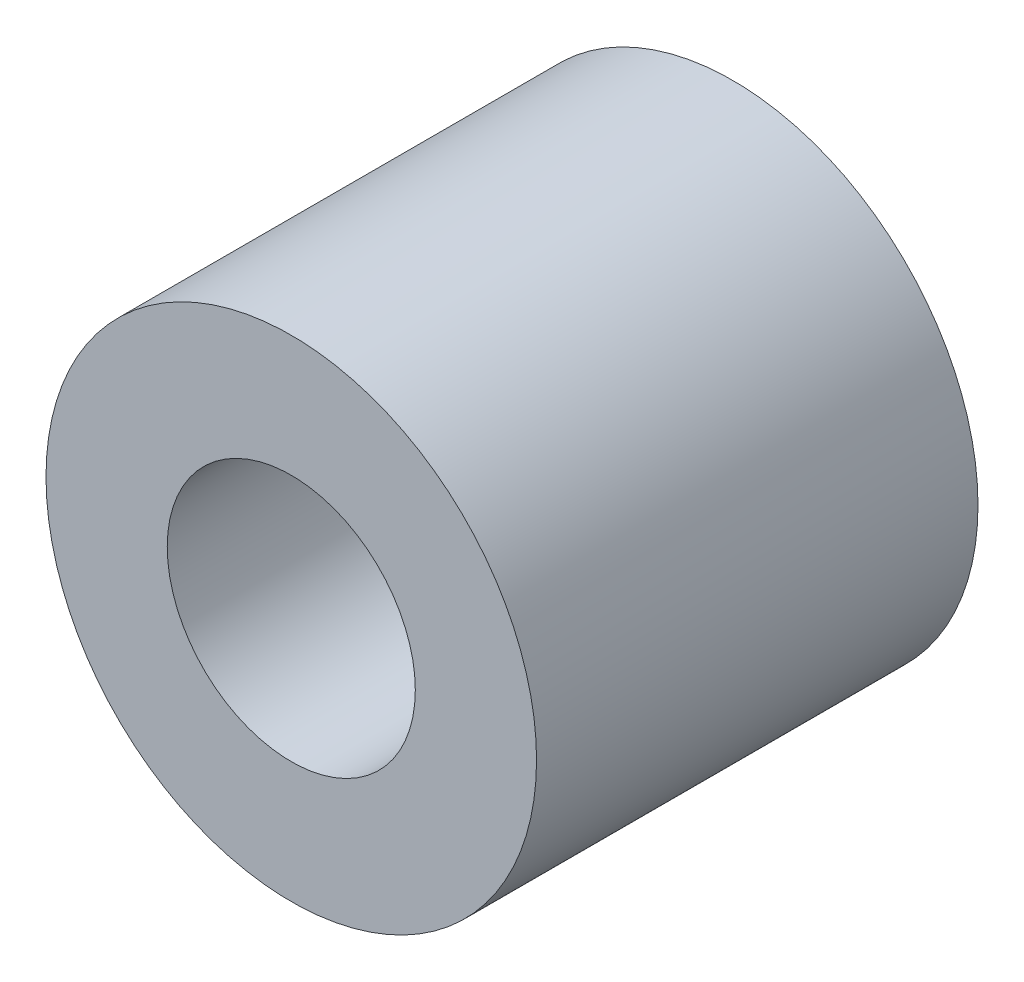
SolidWorks part; units mm, degrees
ref_plane "Front Plane" through (0, 0, 0) normal (0, 0, 1) x (1, 0, 0)
ref_plane "Top Plane" through (0, 0, 0) normal (0, 1, 0) x (1, 0, 0)
ref_plane "Right Plane" through (0, 0, 0) normal (1, 0, 0) x (0, 0, -1)
sketch "Sketch1" plane through (0, 0, 0) normal (0, 0, 1) x (1, 0, 0)
  circle A0 centre (0, 0) radius 4.445
  dimension "D1" = 8.89
extrude "Boss-Extrude1" add sketch "Sketch1" along normal mid plane 8
hole_wizard "#8 Clearance Hole1" positions "Sketch2" profile "Sketch3" hole size "#8" standard "ANSI Inch" end condition through all
sketch "Sketch2" plane through (0, 0, 4) normal (0, 0, 1) x (1, 0, 0)
  point P0 (0, 0)
sketch "Sketch3" plane through (0, 0, 4) normal (1, 0, 0) x (0, -1, 0)
  line L0 (0, 0) -> (0, 8)
  line L1 (0, 8) -> (2.2479, 8)
  line L2 (2.2479, 8) -> (2.2479, 0)
  line L5 (2.2479, 0) -> (0, 0)
  line L11 (0, -6.35) -> (0, 107.95) construction
  dimension "Thru Hole Dia." = 4.4958
  dimension "Thru Hole Depth" = 8
